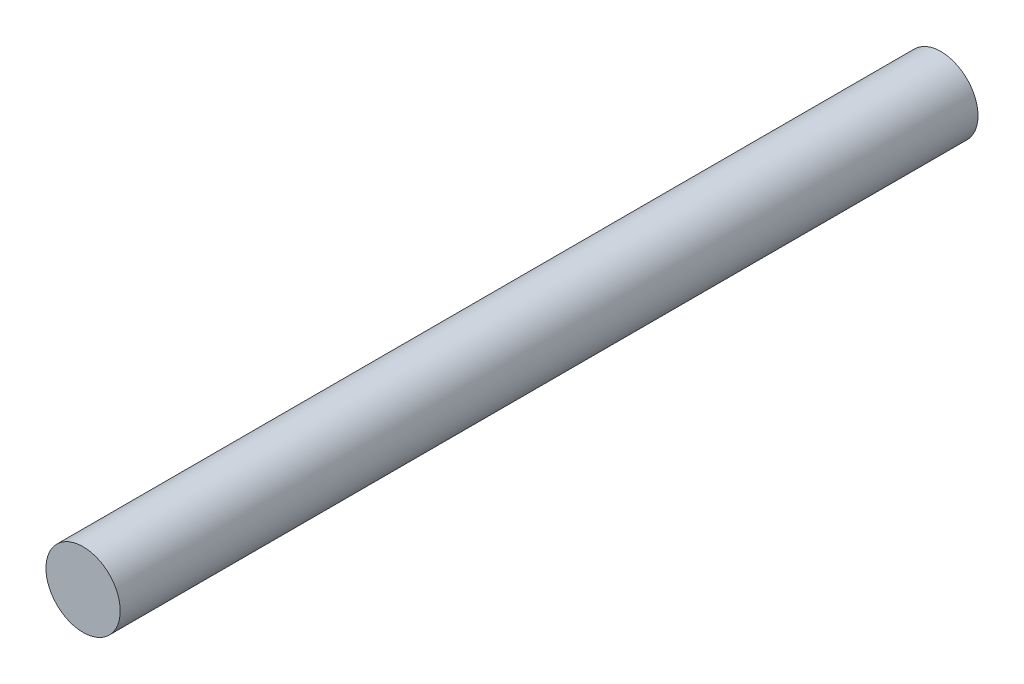
SolidWorks part; units mm, degrees
ref_plane "Front Plane" through (0, 0, 0) normal (0, 0, 1) x (1, 0, 0)
ref_plane "Top Plane" through (0, 0, 0) normal (0, 1, 0) x (1, 0, 0)
ref_plane "Right Plane" through (0, 0, 0) normal (1, 0, 0) x (0, 0, -1)
sketch "Sketch1" plane through (0, 0, 0) normal (0, 0, 1) x (1, 0, 0)
  circle A0 centre (0, 0) radius 5.5
  point P3 (0, 0)
  dimension "D1" = 11
extrude "Boss-Extrude1" add sketch "Sketch1" along normal mid plane 127
